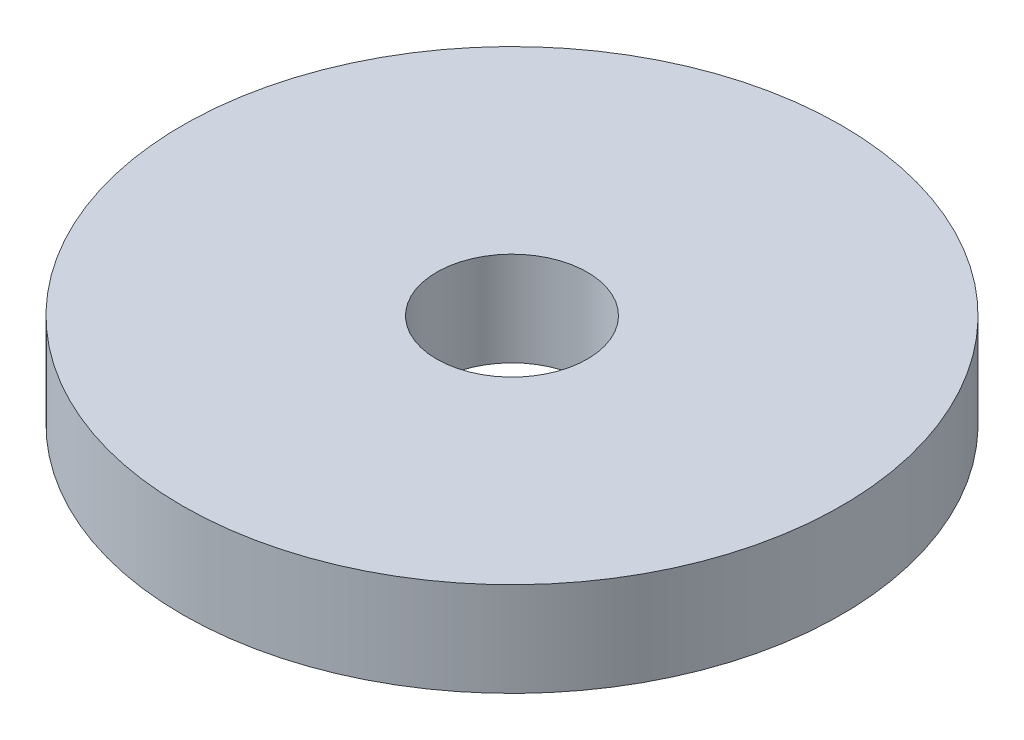
SolidWorks part; units mm, degrees
ref_plane "Front Plane" through (0, 0, 0) normal (0, 0, 1) x (1, 0, 0)
ref_plane "Top Plane" through (0, 0, 0) normal (0, 1, 0) x (1, 0, 0)
ref_plane "Right Plane" through (0, 0, 0) normal (1, 0, 0) x (0, 0, -1)
sketch "Sketch1" plane through (0, 0, 0) normal (0, 1, 0) x (1, 0, 0)
  circle A0 centre (0, 0) radius 7
  circle A1 centre (0, 0) radius 1.6
  dimension "D1" = 14
  dimension "D2" = 3.2
extrude "Boss-Extrude1" add sketch "Sketch1" along normal blind 2
